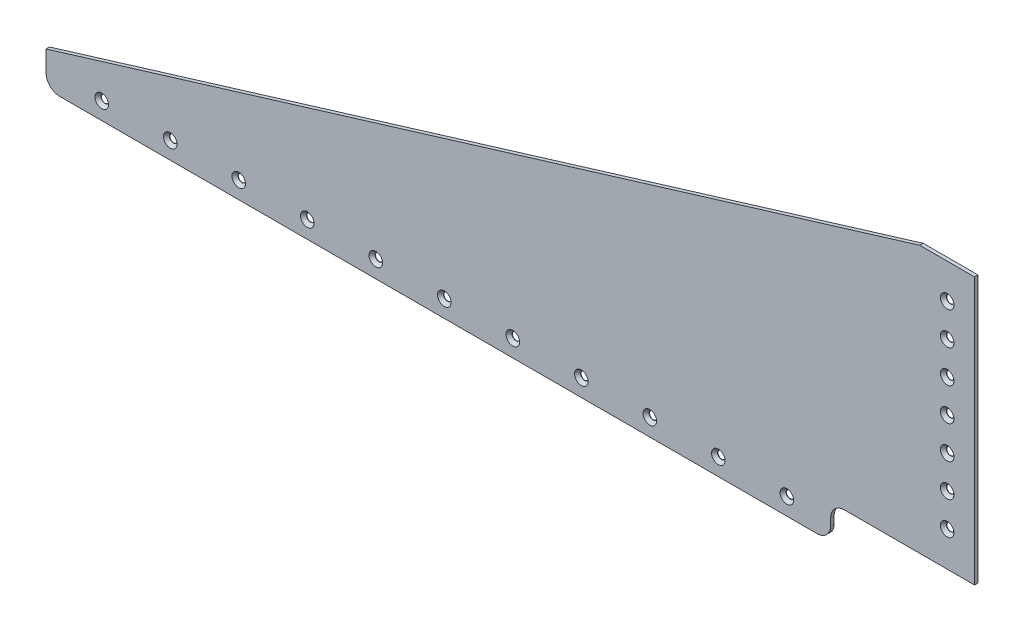
SolidWorks part; units mm, degrees
ref_plane "Front Plane" through (0, 0, 0) normal (0, 0, 1) x (1, 0, 0)
ref_plane "Top Plane" through (0, 0, 0) normal (0, 1, 0) x (1, 0, 0)
ref_plane "Right Plane" through (0, 0, 0) normal (1, 0, 0) x (0, 0, -1)
sketch "Sketch1" plane through (0, 0, 0) normal (0, 0, 1) x (1, 0, 0)
  line L0 (0, 15.875) -> (404.9268, 139.5476)
  line L1 (6.35, 0) -> (357.3018, 0)
  line L2 (0, 6.35) -> (0, 15.875)
  line L3 (404.9268, 139.5476) -> (430.3268, 139.5476)
  line L4 (430.3268, 15.875) -> (430.3268, 139.5476)
  line L6 (363.6518, 6.35) -> (363.6518, 9.525)
  line L7 (370.0018, 15.875) -> (430.3268, 15.875)
  arc A0 (6.35, 0) -> (0, 6.35) centre (6.35, 6.35) cw
  arc A1 (363.6518, 9.525) -> (370.0018, 15.875) centre (370.0018, 9.525) cw
  arc A2 (363.6518, 6.35) -> (357.3018, 0) centre (357.3018, 6.35) cw
  point P10 (0, 0)
  point P13 (363.6518, 15.875)
  point P16 (363.6518, 0)
  dimension "D7" = 6.35
  dimension "D1" = 123.6726
  dimension "D2" = 15.875
  dimension "D3" = 430.3268
  dimension "D4" = 15.875
  dimension "D5" = 25.4
  dimension "D6" = 66.675
extrude "Boss-Extrude1" add sketch "Sketch1" along normal blind 1.5875
hole_wizard "CSK for #6 Flat Head Socket Cap Screw1" positions "Sketch2" profile "Sketch3" countersink size "#6" standard "ANSI Inch"
sketch "Sketch2" plane through (2138.2999, -1688.0331, 1.5875) normal (0, 0, 1) x (1, 0, 0)
  line L0 (-2112.4681, 1695.9706) -> (-1794.9681, 1695.9706) construction
  line L2 (-2131.9499, 1688.0331) -> (-1780.9981, 1688.0331) construction
  point P18 (-1794.9681, 1695.9706)
  point P21 (-1826.7181, 1695.9706)
  point P24 (-1858.4681, 1695.9706)
  point P27 (-1890.2181, 1695.9706)
  point P30 (-1921.9681, 1695.9706)
  point P33 (-1953.7181, 1695.9706)
  point P36 (-1985.4681, 1695.9706)
  point P39 (-2017.2181, 1695.9706)
  point P42 (-2048.9681, 1695.9706)
  point P45 (-2080.7181, 1695.9706)
  point P48 (-2112.4681, 1695.9706)
  dimension "D1" = 7.9375
sketch "Sketch3" plane through (343.3318, 7.9375, 1.5875) normal (1, 0, 0) x (0, -1, 0)
  line L0 (0, 0) -> (0, 2.6229)
  line L1 (0, 2.6229) -> (1.8288, 1.524)
  line L2 (1.8288, 1.524) -> (1.8288, 1.5048)
  line L3 (1.8288, 1.5048) -> (3.1369, 0)
  line L5 (3.1369, 0) -> (0, 0)
  line L6 (-1.8288, 1.5048) -> (-3.1369, 0) construction
  line L10 (0, 2.6229) -> (-1.8288, 1.524) construction
  line L11 (0, -6.35) -> (0, 107.95) construction
  dimension "Hole Dia." = 3.6576
  dimension "Hole Depth" = 1.524
  dimension "Near C'Sink Dia." = 6.2738
  dimension "Near C'Sink Angle" = 82
  dimension "Drill Angle" = 118
hole_wizard "CSK for #6 Flat Head Socket Cap Screw2" positions "Sketch4" profile "Sketch5" countersink size "#6" standard "ANSI Inch"
sketch "Sketch4" plane through (2158.143, -1630.1255, 1.5875) normal (0, 0, 1) x (1, 0, 0)
  point P0 (-1740.5162, 1753.5568)
  point P3 (-1740.5162, 1738.3168)
  point P6 (-1740.5162, 1723.0768)
  point P9 (-1740.5162, 1707.8368)
  point P12 (-1740.5162, 1692.5968)
  point P15 (-1740.5162, 1677.3568)
  point P18 (-1740.5162, 1662.1168)
sketch "Sketch5" plane through (417.6268, 123.4313, 1.5875) normal (1, 0, 0) x (0, -1, 0)
  line L0 (0, 0) -> (0, 2.6229)
  line L1 (0, 2.6229) -> (1.8288, 1.524)
  line L2 (1.8288, 1.524) -> (1.8288, 1.5048)
  line L3 (1.8288, 1.5048) -> (3.1369, 0)
  line L5 (3.1369, 0) -> (0, 0)
  line L6 (-1.8288, 1.5048) -> (-3.1369, 0) construction
  line L10 (0, 2.6229) -> (-1.8288, 1.524) construction
  line L11 (0, -6.35) -> (0, 107.95) construction
  dimension "Hole Dia." = 3.6576
  dimension "Hole Depth" = 1.524
  dimension "Near C'Sink Dia." = 6.2738
  dimension "Near C'Sink Angle" = 82
  dimension "Drill Angle" = 118
